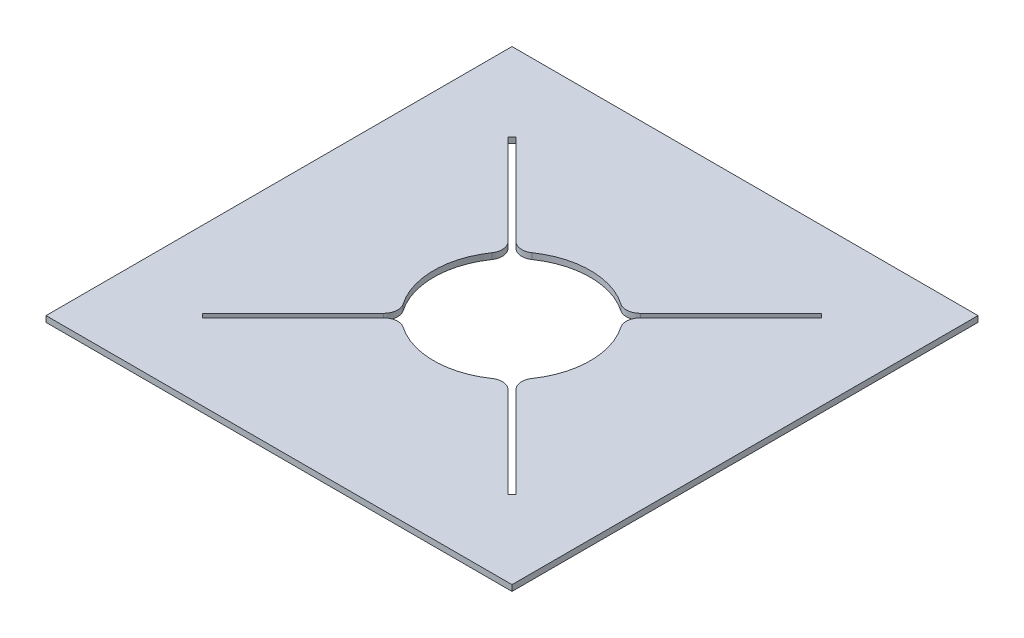
SolidWorks part; units mm, degrees
ref_plane "Front Plane" through (0, 0, 0) normal (0, 0, 1) x (1, 0, 0)
ref_plane "Top Plane" through (0, 0, 0) normal (0, 1, 0) x (1, 0, 0)
ref_plane "Right Plane" through (0, 0, 0) normal (1, 0, 0) x (0, 0, -1)
sketch "Sketch1" plane through (0, 0, 0) normal (0, 1, 0) x (1, 0, 0)
  line L1 (-201.9624, 164.5437) -> (298.0376, 164.5437)
  line L2 (-201.9624, 164.5437) -> (-201.9624, -335.4563)
  line L3 (-201.9624, -335.4563) -> (298.0376, -335.4563)
  line L4 (298.0376, 164.5437) -> (298.0376, -335.4563)
  dimension "D1" = 500
  dimension "D2" = 500
extrude "Boss-Extrude1" add sketch "Sketch1" along normal blind 6.35
sketch "Sketch2" plane through (0, 6.35, 0) normal (0, 1, 0) x (1, 0, 0)
  circle A0 centre (48.0376, -85.4563) radius 84
  dimension "D1" = 168
extrude "Cut-Extrude1" cut sketch "Sketch2" against normal blind 6.35
sketch "Sketch3" plane through (0, 6.35, 0) normal (0, 1, 0) x (1, 0, 0)
  line L0 (48.0376, -85.4563) -> (-118.1325, 80.7138)
  line L1 (216.329, 78.5925) -> (103.1919, -34.5446)
  line L2 (-120.2538, 78.5925) -> (-116.0112, 82.8351)
  line L3 (-120.2538, 78.5925) -> (-7.1167, -34.5446)
  line L4 (-7.1167, -34.5446) -> (-2.8741, -30.3019)
  line L5 (-116.0112, 82.8351) -> (-2.8741, -30.3019)
  line L6 (212.0864, 82.8351) -> (98.9493, -30.3019)
  line L7 (98.9493, -30.3019) -> (103.1919, -34.5446)
  line L8 (212.0864, 82.8351) -> (216.329, 78.5925)
  line L9 (212.0864, -253.7477) -> (98.9493, -140.6106)
  line L10 (216.329, -249.505) -> (103.1919, -136.368)
  line L11 (103.1919, -136.368) -> (98.9493, -140.6106)
  line L12 (216.329, -249.505) -> (212.0864, -253.7477)
  line L13 (-120.2538, -249.505) -> (-7.1167, -136.368)
  line L14 (-116.0112, -253.7477) -> (-2.8741, -140.6106)
  line L15 (-2.8741, -140.6106) -> (-7.1167, -136.368)
  line L16 (-116.0112, -253.7477) -> (-120.2538, -249.505)
  point P2 (-4.9954, -32.4233)
  point P23 (48.0376, -85.4563)
  dimension "D1" = 235
  dimension "D2" = 0
  dimension "D3" = 0
  dimension "D4" = 160
  dimension "D5" = 6
  dimension "D6" = 4
extrude "Cut-Extrude3" cut sketch "Sketch3" against normal blind 6.35 contours L6 L7 L1 L8 | L5 L4 L3 L2 | L15 L13 L16 L14 | L9 L11 L10 L12
fillet "Fillet1" radius 15 8 edges at (105.2754, 3.175, 23.9759) (109.518, 3.175, 28.2185) (109.518, 3.175, 142.694) (105.2754, 3.175, 146.9367) (-9.2002, 3.175, 146.9367) (-13.4428, 3.175, 142.694) (-13.4428, 3.175, 28.2185) (-9.2002, 3.175, 23.9759)
sketch "Sketch4" plane through (0, 6.35, 0) normal (0, 1, 0) x (1, 0, 0)
  line L4 (-201.9624, 164.5437) -> (-201.9624, -335.4563)
  line L5 (-201.9624, -335.4563) -> (298.0376, -335.4563)
  line L6 (298.0376, -335.4563) -> (298.0376, 164.5437)
  line L7 (298.0376, 164.5437) -> (-201.9624, 164.5437)
  line L8 (-201.9624, 164.5437) -> (-201.9624, -335.4563)
  line L9 (-201.9624, -335.4563) -> (298.0376, -335.4563)
  line L10 (298.0376, -335.4563) -> (298.0376, 164.5437)
  line L11 (298.0376, 164.5437) -> (-201.9624, 164.5437)
  line L32 (-119.971, 78.5925) -> (-116.0112, 82.5523)
  line L33 (-116.0112, 82.5523) -> (-18.8193, -14.6396)
  line L34 (212.0864, 82.5523) -> (114.8945, -14.6396)
  line L35 (212.0864, 82.5523) -> (216.0462, 78.5925)
  line L36 (216.0462, 78.5925) -> (118.8543, -18.5994)
  line L37 (216.0462, -249.505) -> (118.8543, -152.3131)
  line L38 (216.0462, -249.505) -> (212.0864, -253.4648)
  line L39 (212.0864, -253.4648) -> (114.8945, -156.2729)
  line L40 (-116.0112, -253.4648) -> (-18.8193, -156.2729)
  line L41 (-116.0112, -253.4648) -> (-119.971, -249.505)
  line L42 (-119.971, -249.505) -> (-22.7791, -152.3131)
  line L43 (-119.971, 78.5925) -> (-22.7791, -18.5994)
  arc A24 (-18.8193, -14.6396) -> (0.5435, -16.4147) centre (-8.0712, -3.8916) ccw
  arc A25 (95.5318, -16.4147) -> (0.5435, -16.4147) centre (48.0376, -85.4563) ccw
  arc A26 (95.5318, -16.4147) -> (114.8945, -14.6396) centre (104.1464, -3.8916) ccw
  arc A27 (118.8543, -18.5994) -> (117.0792, -37.9621) centre (129.6023, -29.3474) ccw
  arc A28 (117.0792, -132.9504) -> (117.0792, -37.9621) centre (48.0376, -85.4563) ccw
  arc A29 (117.0792, -132.9504) -> (118.8543, -152.3131) centre (129.6023, -141.5651) ccw
  arc A30 (114.8945, -156.2729) -> (95.5318, -154.4979) centre (104.1464, -167.021) ccw
  arc A31 (0.5435, -154.4979) -> (95.5318, -154.4979) centre (48.0376, -85.4563) ccw
  arc A32 (0.5435, -154.4979) -> (-18.8193, -156.2729) centre (-8.0712, -167.021) ccw
  arc A33 (-22.7791, -152.3131) -> (-21.004, -132.9504) centre (-33.5271, -141.5651) ccw
  arc A34 (-21.004, -37.9621) -> (-21.004, -132.9504) centre (48.0376, -85.4563) ccw
  arc A35 (-21.004, -37.9621) -> (-22.7791, -18.5994) centre (-33.5271, -29.3474) ccw
  dimension "D1" = 0
